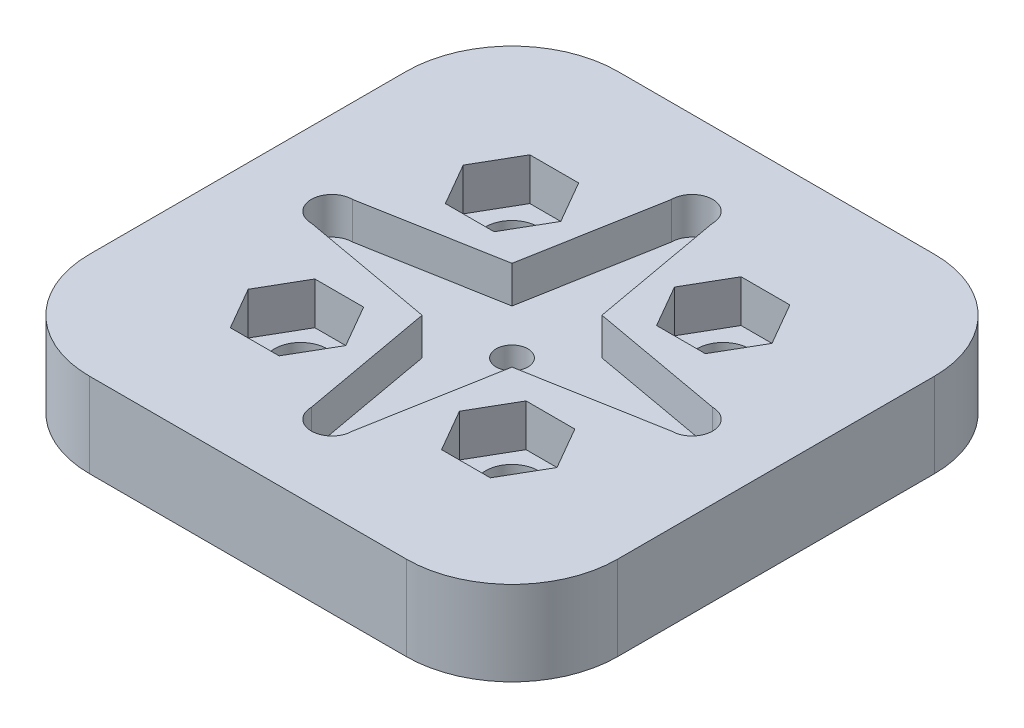
SolidWorks part; units mm, degrees
material "ABS"
ref_plane "Front Plane" through (0, 0, 0) normal (0, 0, 1) x (1, 0, 0)
ref_plane "Top Plane" through (0, 0, 0) normal (0, 1, 0) x (1, 0, 0)
ref_plane "Right Plane" through (0, 0, 0) normal (1, 0, 0) x (0, 0, -1)
sketch "Sketch1" plane through (0, 0, 0) normal (0, 1, 0) x (1, 0, 0)
  line L1 (-25, -25) -> (25, -25)
  line L2 (-25, -25) -> (-25, 25)
  line L3 (-25, 25) -> (25, 25)
  line L4 (25, -25) -> (25, 25)
  line L5 (-25, -25) -> (25, 25) construction
  line L6 (-25, 25) -> (25, -25) construction
  point P0 (0, 0)
  dimension "D1" = 50
extrude "Boss-Extrude1" add sketch "Sketch1" along normal blind 8
sketch "Sketch4" plane through (0, 8, 0) normal (0, 1, 0) x (1, 0, 0)
  line L0 (25, 25) -> (-25, 25) construction
  line L1 (-25, 25) -> (-25, -25) construction
  circle A0 centre (-10, 10) radius 2.5
  dimension "D1" = 5
  dimension "D2" = 15
  dimension "D3" = 15
extrude "Cut-Extrude2" cut sketch "Sketch4" against normal through all
pattern_linear "LPattern1" count 2 spacing 20 along (1, 0, 0) count 2 spacing 20 along (0, 0, 1) of "Cut-Extrude2"
fillet "Fillet2" radius 10 4 edges at (25, 4, 25) (-25, 4, 25) (-25, 4, -25) (25, 4, -25)
sketch "Sketch6" plane through (0, 8, 0) normal (0, 1, 0) x (1, 0, 0)
  line L0 (-4.2562, 4.2562) -> (-1.95, 17.05)
  line L1 (1.95, 17.05) -> (4.2562, 4.2562)
  line L2 (4.2562, 4.2562) -> (17.05, 1.95)
  line L3 (17.05, -1.95) -> (4.2562, -4.2562)
  line L4 (4.2562, -4.2562) -> (1.95, -17.05)
  line L5 (-1.95, -17.05) -> (-4.2562, -4.2562)
  line L6 (-4.2562, -4.2562) -> (-17.05, -1.95)
  line L7 (-17.05, 1.95) -> (-4.2562, 4.2562)
  line L8 (-17.05, 1.95) -> (-17.05, -1.95) construction
  line L9 (17.05, 1.95) -> (17.05, -1.95) construction
  line L10 (-1.95, 17.05) -> (1.95, 17.05) construction
  line L11 (-1.95, -17.05) -> (1.95, -17.05) construction
  arc A0 (-1.95, 17.05) -> (1.95, 17.05) centre (0, 17.05) cw
  arc A1 (17.05, 1.95) -> (17.05, -1.95) centre (17.05, 0) cw
  arc A2 (1.95, -17.05) -> (-1.95, -17.05) centre (0, -17.05) cw
  arc A4 (-17.05, -1.95) -> (-17.05, 1.95) centre (-17.05, 0) cw
  point P2 (19, 0)
  point P3 (0, 19)
  point P6 (0, -19)
  point P20 (-19, 0)
  dimension "D1" = 1.95
  dimension "D2" = 1.95
  dimension "D3" = 1.95
  dimension "D4" = 1.95
  dimension "D5" = 13
  dimension "D6" = 19
  dimension "D7" = 19
  dimension "D8" = 19
  dimension "D9" = 19
  dimension "D10" = 3.9
extrude "Cut-Extrude4" cut sketch "Sketch6" against normal blind 3.5
sketch "Sketch7" plane through (0, 4.5, 0) normal (0, 1, 0) x (1, 0, 0)
  circle A0 centre (0, 0) radius 4 construction
  dimension "D1" = 8
sketch "Sketch8" plane through (0, 0, 0) normal (0, -1, 0) x (1, 0, 0)
  circle A0 centre (0, 0) radius 1.5
  dimension "D1" = 3
extrude "Cut-Extrude5" cut sketch "Sketch8" against normal up to surface (8 mm away) up to face at (0, 8, 0)
sketch "Sketch9" plane through (0, 8, 0) normal (0, 1, 0) x (1, 0, 0)
  line L0 (14.6188, 10) -> (12.3094, 14)
  line L1 (-7.6906, 14) -> (-12.3094, 14)
  line L2 (-12.3094, 14) -> (-14.6188, 10)
  line L3 (-14.6188, 10) -> (-12.3094, 6)
  line L4 (-12.3094, 6) -> (-7.6906, 6)
  line L5 (-7.6906, 6) -> (-5.3812, 10)
  line L6 (-5.3812, 10) -> (-7.6906, 14)
  line L7 (12.3094, 6) -> (14.6188, 10)
  line L8 (7.6906, 6) -> (12.3094, 6)
  line L9 (5.3812, 10) -> (7.6906, 6)
  line L10 (7.6906, 14) -> (5.3812, 10)
  line L11 (12.3094, 14) -> (7.6906, 14)
  line L12 (14.6188, -10.3599) -> (12.3094, -6.3599)
  line L13 (12.3094, -14.3599) -> (14.6188, -10.3599)
  line L14 (7.6906, -14.3599) -> (12.3094, -14.3599)
  line L15 (5.3812, -10.3599) -> (7.6906, -14.3599)
  line L16 (7.6906, -6.3599) -> (5.3812, -10.3599)
  line L17 (12.3094, -6.3599) -> (7.6906, -6.3599)
  line L18 (-5.3812, -10.3599) -> (-7.6906, -6.3599)
  line L19 (-7.6906, -14.3599) -> (-5.3812, -10.3599)
  line L20 (-12.3094, -14.3599) -> (-7.6906, -14.3599)
  line L21 (-14.6188, -10.3599) -> (-12.3094, -14.3599)
  line L22 (-12.3094, -6.3599) -> (-14.6188, -10.3599)
  line L23 (-7.6906, -6.3599) -> (-12.3094, -6.3599)
  circle A0 centre (-10, 10) radius 4 construction
  point P1 (-10, -6.3599)
  dimension "D1" = 8
  dimension "D4" = 20
  dimension "D2" = 2
  dimension "D3" = 2
extrude "Cut-Extrude6" cut sketch "Sketch9" against normal blind 4
